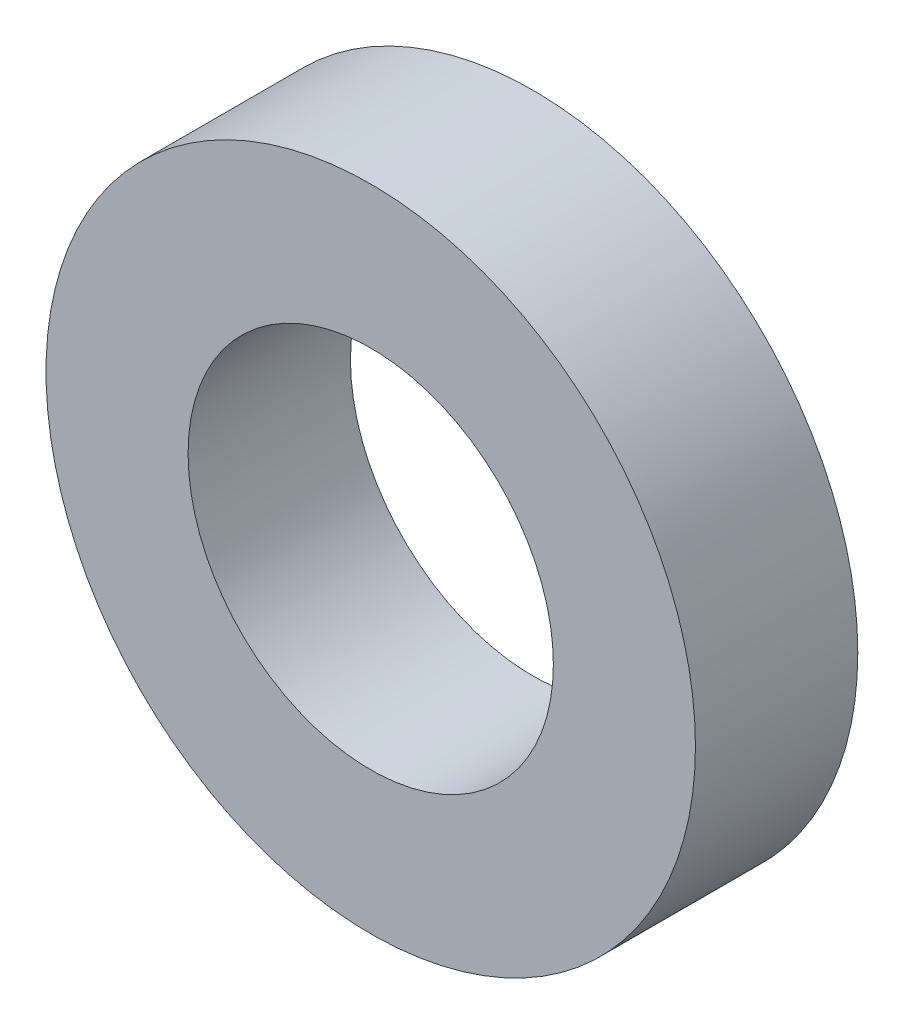
SolidWorks part; units mm, degrees
material "ABS"
ref_plane "前视基准面" through (0, 0, 0) normal (0, 0, 1) x (1, 0, 0)
ref_plane "上视基准面" through (0, 0, 0) normal (0, 1, 0) x (1, 0, 0)
ref_plane "右视基准面" through (0, 0, 0) normal (1, 0, 0) x (0, 0, -1)
sketch "草图1" plane through (0, 0, 0) normal (0, 0, 1) x (1, 0, 0)
  circle A0 centre (0, 0) radius 2.25
  circle A1 centre (0, 0) radius 4
  dimension "D1" = 4.5
  dimension "D2" = 8
extrude "凸台-拉伸1" add sketch "草图1" along normal blind 2
